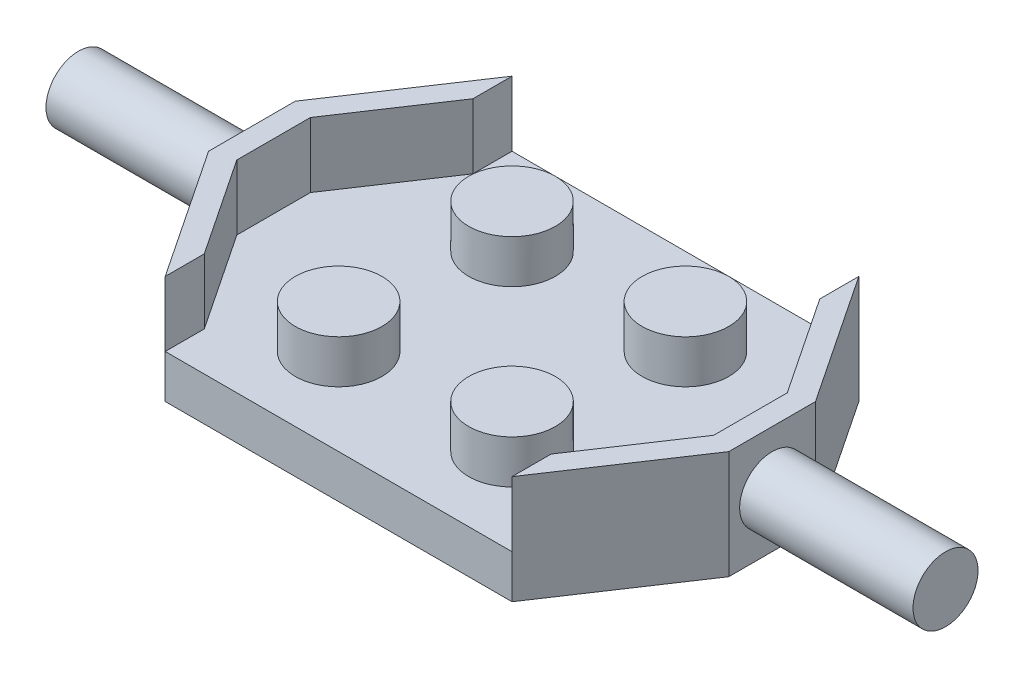
SolidWorks part; units mm, degrees
ref_plane "Front Plane" through (0, 0, 0) normal (0, 0, 1) x (1, 0, 0)
ref_plane "Top Plane" through (0, 0, 0) normal (0, 1, 0) x (1, 0, 0)
ref_plane "Right Plane" through (0, 0, 0) normal (1, 0, 0) x (0, 0, -1)
sketch "Sketch1" plane through (0, 0, 0) normal (0, 1, 0) x (1, 0, 0)
  line L0 (0, 0) -> (-12, 0) construction
  line L1 (-12, -2) -> (-12, 2)
  line L2 (-12, 2) -> (-8, 8)
  line L3 (-8, 8) -> (0, 8)
  line L4 (0, 8) -> (0, -8)
  line L5 (-8, -8) -> (0, -8)
  line L6 (-12, -2) -> (-8, -8)
  dimension "D1" = 12
  dimension "D2" = 8
  dimension "D3" = 8
  dimension "D4" = 2
extrude "Boss-Extrude1" add sketch "Sketch1" along normal blind 2
sketch "Sketch2" plane through (0, 2, 0) normal (0, 1, 0) x (1, 0, 0)
  line L0 (0, 0) -> (-12.8096, 0) construction
  line L1 (0, 8) -> (-8, 8) construction
  line L2 (0, -8) -> (0, 8) construction
  circle A0 centre (-4, 4) radius 2
  circle A1 centre (-4, -4) radius 2
  dimension "D1" = 4
  dimension "D2" = 4
  dimension "D3" = 4
extrude "Boss-Extrude2" add sketch "Sketch2" along normal blind 2
sketch "Sketch3" plane through (0, 2, 0) normal (0, 1, 0) x (1, 0, 0)
  line L0 (-12, 2) -> (-12, -2) construction
  line L1 (-8, 8) -> (-12, 2) construction
  line L2 (-12, -2) -> (-8, -8) construction
  line L3 (-12, -2) -> (-8, -8)
  line L4 (-12, 2) -> (-12, -2)
  line L5 (-8, 8) -> (-12, 2)
  line L6 (-8, 6.1972) -> (-11, 1.6972)
  line L7 (-11, 1.6972) -> (-11, -1.6972)
  line L8 (-11, -1.6972) -> (-8, -6.1972)
  line L9 (-8, -8) -> (-8, -6.1972)
  line L10 (-8, 6.1972) -> (-8, 8)
  line L11 (-7.1679, 7.4453) -> (-11, 1.6972) construction
  line L12 (-11, -1.6972) -> (-7.1679, -7.4453) construction
  dimension "D1" = 1
extrude "Boss-Extrude3" add sketch "Sketch3" along normal blind 3
sketch "Sketch4" plane through (-12, 0, 0) normal (-1, 0, 0) x (0, 0, 1)
  line L1 (0, 0) -> (0, 5) construction
  line L2 (-2, 5) -> (2, 5) construction
  line L5 (-2, 0) -> (2, 0) construction
  line L6 (-2, 5) -> (-2, 0) construction
  circle A0 centre (0, 2.5) radius 1.5
  point P7 (0, 0)
  point P12 (0, 0)
  point P13 (0, 0)
  dimension "D1" = 3
  dimension "D2" = 2.5
  dimension "D3" = 2
extrude "Boss-Extrude4" add sketch "Sketch4" along normal blind 8
mirror "Mirror2" about plane through (0, 0, 0) normal (1, 0, 0) of bodies 104
